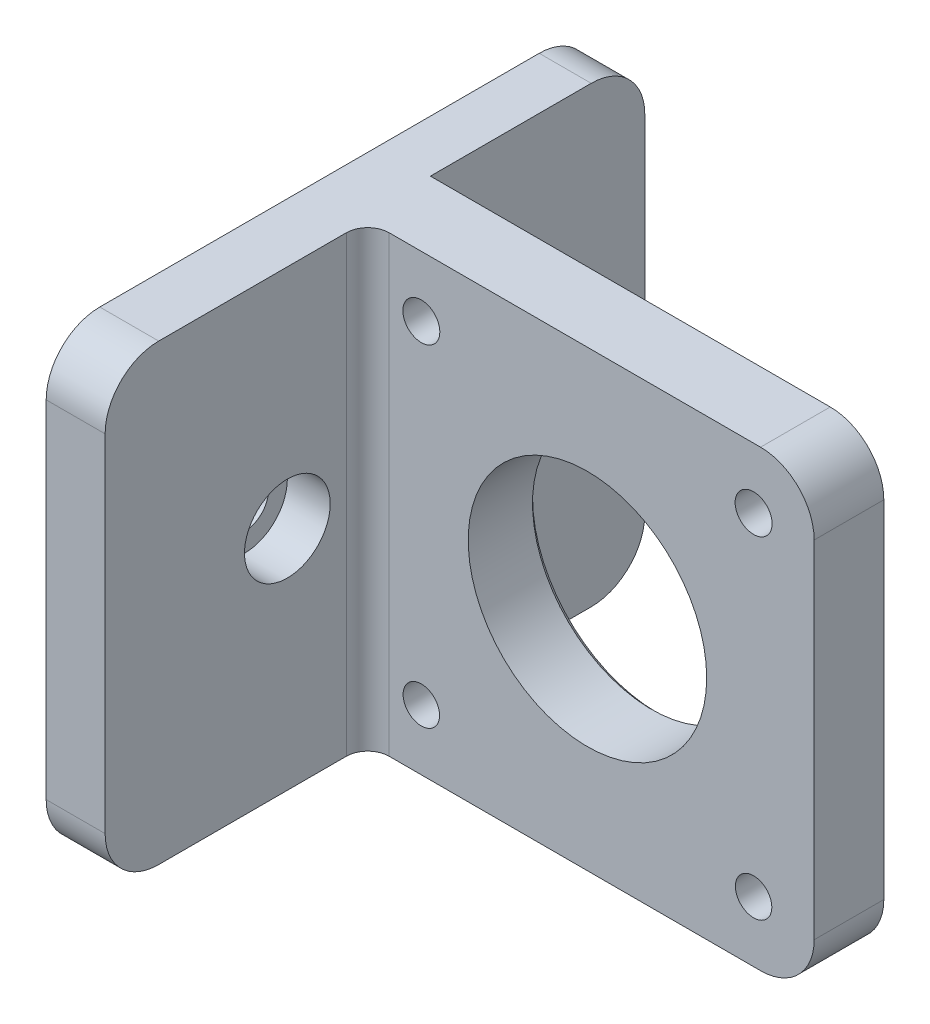
SolidWorks part; units mm, degrees
material "ABS PC"
ref_plane "Front Plane" through (0, 0, 0) normal (0, 0, 1) x (1, 0, 0)
ref_plane "Top Plane" through (0, 0, 0) normal (0, 1, 0) x (1, 0, 0)
ref_plane "Right Plane" through (0, 0, 0) normal (1, 0, 0) x (0, 0, -1)
sketch "Sketch1" plane through (0, 0, 0) normal (0, 0, 1) x (1, 0, 0)
  line L1 (-21.15, 21.15) -> (21.15, 21.15)
  line L2 (-21.15, 21.15) -> (-21.15, -21.15)
  line L3 (-21.15, -21.15) -> (21.15, -21.15)
  line L4 (21.15, 21.15) -> (21.15, -21.15)
  line L5 (-21.15, 21.15) -> (21.15, -21.15) construction
  line L6 (-21.15, -21.15) -> (21.15, 21.15) construction
  point P0 (0, 0)
  dimension "D1" = 42.3
  dimension "D2" = 42.3
extrude "Boss-Extrude1" add sketch "Sketch1" along normal mid plane 4
sketch "Sketch2" plane through (0, 0, 2) normal (0, 0, 1) x (1, 0, 0)
  line L1 (-15.5, 15.5) -> (15.5, 15.5)
  line L2 (-15.5, 15.5) -> (-15.5, -15.5)
  line L3 (-15.5, -15.5) -> (15.5, -15.5)
  line L4 (15.5, 15.5) -> (15.5, -15.5)
  line L5 (-15.5, 15.5) -> (15.5, -15.5) construction
  line L6 (-15.5, -15.5) -> (15.5, 15.5) construction
  point P0 (0, 0)
  dimension "D1" = 31
  dimension "D2" = 31
hole_wizard "M3 Clearance Hole1" positions "Sketch5" profile "Sketch4" hole size "M3" standard "ANSI Metric" end condition through all
sketch "Sketch5" plane through (0, 0, 2) normal (0, 0, 1) x (1, 0, 0)
  point P0 (-15.5, 15.5)
  point P3 (15.5, 15.5)
  point P6 (15.5, -15.5)
  point P9 (-15.5, -15.5)
sketch "Sketch4" plane through (-15.5, 15.5, 2) normal (1, 0, 0) x (0, -1, 0)
  line L0 (0, 0) -> (0, 4)
  line L1 (0, 4) -> (1.7, 4)
  line L2 (1.7, 4) -> (1.7, 0.025)
  line L3 (1.7, 0.025) -> (1.725, 0)
  line L5 (1.725, 0) -> (0, 0)
  line L6 (-1.7, 0.025) -> (-1.725, 0) construction
  line L11 (0, -6.35) -> (0, 107.95) construction
  dimension "Thru Hole Dia." = 3.4
  dimension "Thru Hole Depth" = 4
  dimension "Near C'Sink Dia." = 3.45
  dimension "Near C'Sink Angle" = 90
sketch "Sketch6" plane through (0, 0, 2) normal (0, 0, 1) x (1, 0, 0)
  circle A0 centre (0, 0) radius 11.125
  dimension "D1" = 22.25
extrude "Cut-Extrude1" cut sketch "Sketch6" against normal through all
sketch "Sketch9" plane through (0, 0, 0) normal (0, 0, 1) x (1, 0, 0)
  line L0 (-21.15, -21.15) -> (21.15, -21.15) construction
  line L1 (-21.15, 21.15) -> (-26, 21.15)
  line L2 (-21.15, 21.15) -> (-21.15, -21.15)
  line L3 (-21.15, -21.15) -> (-26, -21.15)
  line L4 (-26, 21.15) -> (-26, -21.15)
  line L5 (21.15, 21.15) -> (-21.15, 21.15) construction
  line L6 (-21.15, 21.15) -> (-21.15, -21.15) construction
  dimension "D1" = 4.85
extrude "Boss-Extrude2" add sketch "Sketch9" along normal mid plane 30
fillet "Fillet2" radius 5 2 edges at (21.15, -21.15, 0) (21.15, 21.15, 0)
sketch "Sketch13" plane through (0, 0, -15) normal (0, 0, -1) x (-1, 0, 0)
  line L4 (21.15, 21.15) -> (21.15, -21.15)
  line L5 (21.15, -21.15) -> (26, -21.15)
  line L6 (26, -21.15) -> (26, 21.15)
  line L7 (26, 21.15) -> (21.15, 21.15)
  line L8 (21.15, 21.15) -> (21.15, -21.15)
  line L9 (21.15, -21.15) -> (26, -21.15)
  line L10 (26, -21.15) -> (26, 21.15)
  line L11 (26, 21.15) -> (21.15, 21.15)
  dimension "D1" = 0
extrude "Boss-Extrude4" add sketch "Sketch13" along normal blind 7
sketch "Sketch14" plane through (0, 0, 15) normal (0, 0, 1) x (1, 0, 0)
  line L4 (-21.15, -21.15) -> (-21.15, 21.15)
  line L5 (-21.15, 21.15) -> (-26, 21.15)
  line L6 (-26, 21.15) -> (-26, -21.15)
  line L7 (-26, -21.15) -> (-21.15, -21.15)
  line L8 (-21.15, -21.15) -> (-21.15, 21.15)
  line L9 (-21.15, 21.15) -> (-26, 21.15)
  line L10 (-26, 21.15) -> (-26, -21.15)
  line L11 (-26, -21.15) -> (-21.15, -21.15)
  dimension "D1" = 0
extrude "Boss-Extrude5" add sketch "Sketch14" along normal blind 14
sketch "Sketch15" plane through (-21.15, 0, 0) normal (1, 0, 0) x (0, 0, -1)
  line L0 (2, 0) -> (22, 0) construction
  line L1 (2, -16.15) -> (2, 16.15) construction
  line L2 (22, 16.15) -> (22, -16.15) construction
  line L3 (0, 23.265) -> (0, -23.265) construction
  line L4 (-2, 0) -> (-22, 0) construction
  point P6 (12, 0)
  point P9 (-12, 0)
hole_wizard "CBORE for M4 SHCS1" positions "Sketch20" profile "Sketch17" counterbore size "M4" standard "ANSI Metric"
sketch "Sketch20" plane through (-21.15, 0, 0) normal (1, 0, 0) x (0, 0, -1)
  point P0 (-12, 0)
  point P3 (12, 0)
sketch "Sketch17" plane through (-21.15, 0, -12) normal (0, 1, 0) x (0, 0, -1)
  line L0 (0, 0) -> (0, 4.85)
  line L1 (0, 4.85) -> (2.25, 4.85)
  line L3 (2.25, 4.85) -> (2.25, 4)
  line L4 (2.25, 4) -> (4, 4)
  line L5 (4, 4) -> (4, 0)
  line L7 (4, 0) -> (0, 0)
  line L11 (0, -6.35) -> (0, 107.95) construction
  dimension "Thru Hole Dia." = 4.5
  dimension "Thru Hole Depth" = 4.85
  dimension "C'Bore Dia." = 8
  dimension "C'Bore Depth" = 4
fillet "Fillet3" radius 5 4 edges at (-23.575, 21.15, 29) (-23.575, 21.15, -22) (-23.575, -21.15, -22) (-23.575, -21.15, 29)
fillet "Fillet4" [suppressed] radius 2.5
sketch "Sketch19" plane through (0, 0, 2) normal (0, 0, 1) x (1, 0, 0)
  line L4 (-21.15, -21.15) -> (16.15, -21.15)
  line L5 (21.15, -16.15) -> (21.15, 16.15)
  line L6 (16.15, 21.15) -> (-21.15, 21.15)
  line L7 (-21.15, 21.15) -> (-21.15, -21.15)
  line L8 (-21.15, -21.15) -> (16.15, -21.15)
  line L9 (21.15, -16.15) -> (21.15, 16.15)
  line L10 (16.15, 21.15) -> (-21.15, 21.15)
  line L11 (-21.15, 21.15) -> (-21.15, -21.15)
  circle A0 centre (-15.5, -15.5) radius 1.7 construction
  circle A1 centre (0, 0) radius 11.125
  circle A2 centre (0, 0) radius 11.125
  circle A3 centre (15.5, 15.5) radius 1.725
  circle A4 centre (15.5, 15.5) radius 1.725
  circle A5 centre (-15.5, 15.5) radius 1.725
  circle A6 centre (-15.5, 15.5) radius 1.725
  circle A7 centre (15.5, -15.5) radius 1.7 construction
  circle A8 centre (-15.5, -15.5) radius 1.7
  circle A9 centre (15.5, -15.5) radius 1.7
  arc A12 (16.15, -21.15) -> (21.15, -16.15) centre (16.15, -16.15) ccw
  arc A13 (21.15, 16.15) -> (16.15, 21.15) centre (16.15, 16.15) ccw
  arc A14 (16.15, -21.15) -> (21.15, -16.15) centre (16.15, -16.15) ccw
  arc A15 (21.15, 16.15) -> (16.15, 21.15) centre (16.15, 16.15) ccw
  dimension "D1" = 0
  dimension "D2" = 0
  dimension "D3" = 0
  dimension "D4" = 0
extrude "Boss-Extrude6" add sketch "Sketch19" along normal blind 2.5 and the other way up to next (4 mm away)
fillet "Fillet5" [suppressed] radius 2
sketch "Sketch21" plane through (-21.15, 0, 0) normal (1, 0, 0) x (0, 0, -1)
  line L4 (-24, -21.15) -> (-4.5, -21.15)
  line L5 (-4.5, -21.15) -> (-4.5, 21.15)
  line L6 (-4.5, 21.15) -> (-24, 21.15)
  line L7 (-29, 16.15) -> (-29, -16.15)
  line L8 (-24, -21.15) -> (-4.5, -21.15)
  line L9 (-4.5, -21.15) -> (-4.5, 21.15)
  line L10 (-4.5, 21.15) -> (-24, 21.15)
  line L11 (-29, 16.15) -> (-29, -16.15)
  arc A2 (-24, 21.15) -> (-29, 16.15) centre (-24, 16.15) ccw
  arc A3 (-29, -16.15) -> (-24, -21.15) centre (-24, -16.15) ccw
  arc A4 (-24, 21.15) -> (-29, 16.15) centre (-24, 16.15) ccw
  arc A5 (-29, -16.15) -> (-24, -21.15) centre (-24, -16.15) ccw
  dimension "D1" = 0
extrude "Boss-Extrude7" add sketch "Sketch21" along normal blind 0.65
sketch "Sketch25" plane through (-20.5, 0, 0) normal (1, 0, 0) x (0, 0, -1)
  point P0 (-12, 0)
hole_wizard "CBORE for M4 SHCS3" positions "Sketch25" profile "Sketch26" counterbore size "M4" standard "ANSI Metric" end condition through all
sketch "Sketch26" plane through (-20.5, 0, 12) normal (0, 1, 0) x (0, 0, -1)
  line L0 (0, 0) -> (0, 5.5)
  line L1 (0, 5.5) -> (2.25, 5.5)
  line L3 (2.25, 5.5) -> (2.25, 4)
  line L4 (2.25, 4) -> (4, 4)
  line L5 (4, 4) -> (4, 0)
  line L7 (4, 0) -> (0, 0)
  line L11 (0, -6.35) -> (0, 107.95) construction
  dimension "Thru Hole Dia." = 4.5
  dimension "Thru Hole Depth" = 5.5
  dimension "C'Bore Dia." = 8
  dimension "C'Bore Depth" = 4
fillet "Fillet6" radius 2 1 edges at (-20.5, 0, 4.5)
chamfer "Chamfer1" distance 0.5 angle 45 1 edges at (11.125, 0, -2)
equation "\"D2@Sketch1\"=\"D1@Sketch1\""
equation "\"D2@Sketch2\"=\"D1@Sketch2\""
